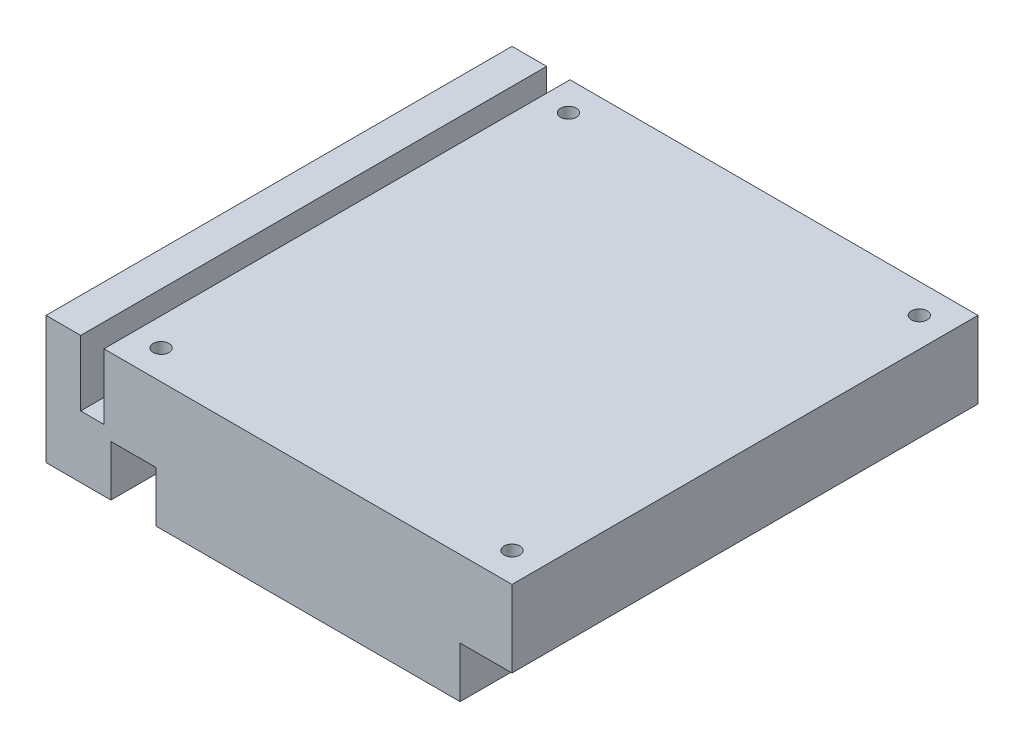
SolidWorks part; units mm, degrees
ref_plane "Front Plane" through (0, 0, 0) normal (0, 0, 1) x (1, 0, 0)
ref_plane "Top Plane" through (0, 0, 0) normal (0, 1, 0) x (1, 0, 0)
ref_plane "Right Plane" through (0, 0, 0) normal (1, 0, 0) x (0, 0, -1)
sketch "Sketch1" plane through (0, 0, 0) normal (0, 1, 0) x (1, 0, 0)
  line L1 (0, 0) -> (104.902, 0)
  line L2 (0, 0) -> (0, 104.902)
  line L3 (0, 104.902) -> (104.902, 104.902)
  line L4 (104.902, 0) -> (104.902, 104.902)
  dimension "D1" = 104.902
extrude "Boss-Extrude1" add sketch "Sketch1" along normal blind 2.54
sketch "Sketch2" plane through (0, 2.54, 0) normal (0, 1, 0) x (1, 0, 0)
  line L0 (104.902, 104.902) -> (0, 104.902) construction
  line L1 (104.902, 0) -> (13.0401, 0)
  line L2 (104.902, 0) -> (104.902, 104.902)
  line L3 (104.902, 104.902) -> (13.0401, 104.902)
  line L4 (13.0401, 0) -> (13.0401, 104.902)
  line L5 (0, 0) -> (104.902, 0) construction
  line L6 (0, 104.902) -> (7.8067, 104.902)
  line L7 (0, 104.902) -> (0, 0)
  line L8 (0, 0) -> (7.8067, 0)
  line L9 (7.8067, 104.902) -> (7.8067, 0)
extrude "Boss-Extrude2" add sketch "Sketch2" along normal blind 14.732
sketch "Sketch3" plane through (0, 17.272, 0) normal (0, 1, 0) x (1, 0, 0)
  line L0 (104.902, 0) -> (104.902, 104.902) construction
  line L1 (13.0401, 0) -> (104.902, 0) construction
  line L2 (104.902, 104.902) -> (13.0401, 104.902) construction
  circle A0 centre (98.298, 6.604) radius 1.778
  circle A1 centre (98.298, 98.298) radius 1.778
  circle A2 centre (19.304, 6.604) radius 1.778
  circle A3 centre (19.304, 98.298) radius 1.778
  dimension "D4" = 3.556
  dimension "D1" = 6.604
  dimension "D2" = 6.604
  dimension "D3" = 6.604
  dimension "D5" = 78.994
extrude "Cut-Extrude1" cut sketch "Sketch3" against normal through all
sketch "Sketch4" plane through (0, 0, 0) normal (0, -1, 0) x (1, 0, 0)
  line L0 (104.902, -104.902) -> (0, -104.902) construction
  line L1 (24.7617, -104.902) -> (93.2208, -104.902)
  line L2 (24.7617, -104.902) -> (24.7617, -90.0828)
  line L3 (24.7617, -90.0828) -> (93.2208, -90.0828)
  line L4 (93.2208, -104.902) -> (93.2208, -90.0828)
  line L5 (0, 0) -> (104.902, 0) construction
  line L6 (24.7617, 0) -> (93.2208, 0)
  line L7 (24.7617, 0) -> (24.7617, -13.5988)
  line L8 (24.7617, -13.5988) -> (93.2208, -13.5988)
  line L9 (93.2208, 0) -> (93.2208, -13.5988)
  line L11 (0, 0) -> (14.6169, 0)
  line L12 (0, 0) -> (0, -13.5988)
  line L13 (0, -13.5988) -> (14.6169, -13.5988)
  line L14 (14.6169, 0) -> (14.6169, -13.5988)
extrude "Boss-Extrude3" add sketch "Sketch4" along normal blind 11.43
sketch "Sketch5" plane through (0, -11.43, 0) normal (0, -1, 0) x (1, 0, 0)
  text T0 "PWR"
  text T1 "HDMI   ESATA      ETH"
  text T2 "GPIO                          USBC"
  text T3 "uUSB\r\n"
